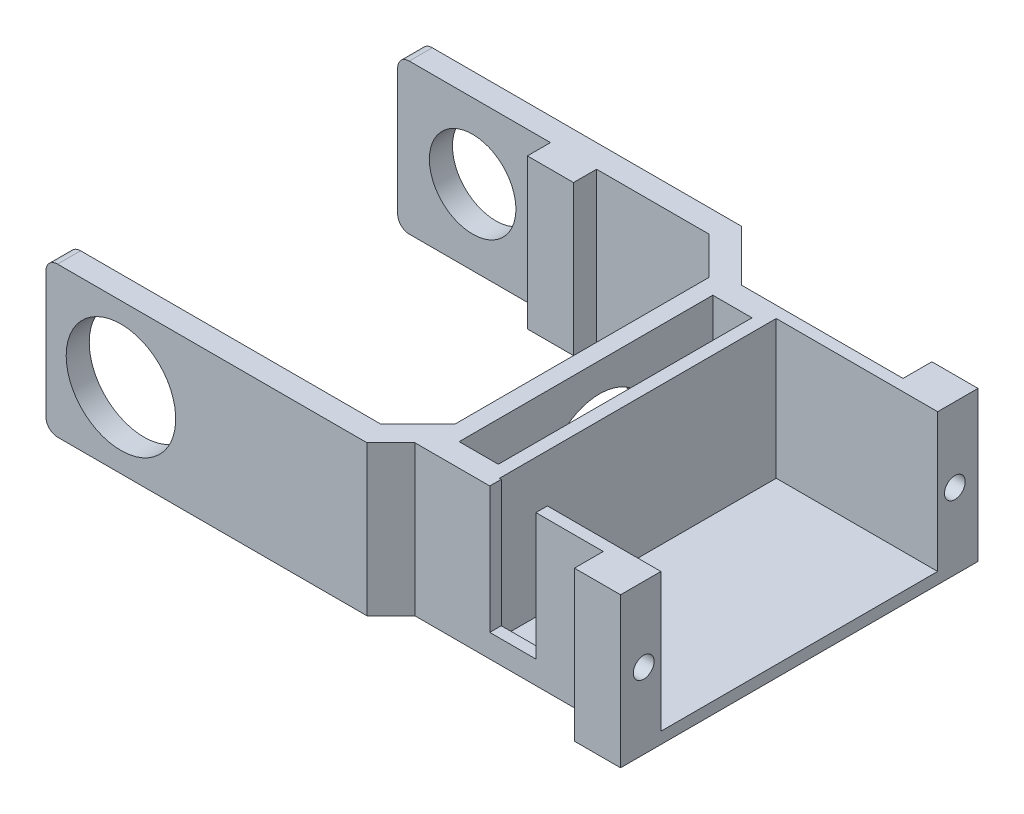
SolidWorks part; units mm, degrees
material "uhlíková ocel 7850"
ref_plane "Přední rovina" through (0, 0, 0) normal (0, 0, 1) x (1, 0, 0)
ref_plane "Horní rovina" through (0, 0, 0) normal (0, 1, 0) x (1, 0, 0)
ref_plane "Pravá rovina" through (0, 0, 0) normal (1, 0, 0) x (0, 0, -1)
sketch "Skica1" plane through (0, 0, 0) normal (0, 1, 0) x (1, 0, 0)
  line L0 (0, -11) -> (0, 11)
  line L1 (0, 11) -> (-3.25, 14.25)
  line L2 (-3.25, 14.25) -> (-30.25, 14.25)
  line L3 (-30.25, 14.25) -> (-30.25, 16.25)
  line L4 (-30.25, 16.25) -> (-2.4216, 16.25)
  line L5 (-2.4216, 16.25) -> (2, 11.8284)
  line L6 (2, 11.8284) -> (2, -11.8284)
  line L7 (2, 0) -> (0, 0) construction
  line L8 (-2.4216, -16.25) -> (2, -11.8284)
  line L9 (-30.25, -16.25) -> (-2.4216, -16.25)
  line L10 (-30.25, -14.25) -> (-30.25, -16.25)
  line L11 (-3.25, -14.25) -> (-30.25, -14.25)
  line L12 (0, -11) -> (-3.25, -14.25)
  dimension "D1" = 11
  dimension "D2" = 135
  dimension "D3" = 27
  dimension "D4" = 2
  dimension "D5" = 2
  dimension "D6" = 2
  dimension "D7" = 14.25
extrude "Přidat vysunutím1" add sketch "Skica1" along normal blind 13
fillet "Zaoblit1" radius 1 4 edges at (-30.25, 0, -15.25) (-30.25, 0, 15.25) (-30.25, 13, 15.25) (-30.25, 13, -15.25)
sketch "Skica6" plane through (0, 0, -16.25) normal (0, 0, -1) x (-1, 0, 0)
  line L0 (23.75, 6.5) -> (30.25, 6.5) construction
  line L1 (30.25, 12) -> (30.25, 1) construction
  circle A0 centre (23.75, 6.5) radius 3.75
  dimension "D1" = 7.5
  dimension "D2" = 6.5
extrude "Odebrat vysunutím4" cut sketch "Skica6" against normal blind 5
sketch "Skica7" plane through (0, 0, 14.25) normal (0, 0, -1) x (-1, 0, 0)
  circle A0 centre (23.75, 6.5) radius 4.75
  dimension "D1" = 9.5
extrude "Odebrat vysunutím5" cut sketch "Skica7" against normal blind 5
sketch "Skica8" plane through (0, 0, 0) normal (0, -1, 0) x (1, 0, 0)
  line L0 (-2.4216, 16.25) -> (2, 11.8284) construction
  line L1 (-0.3431, 14.1716) -> (20, 14.1716)
  line L2 (2, -11.8284) -> (2, 11.8284)
  line L3 (2, -11.8284) -> (20, -11.8284)
  line L4 (20, 14.1716) -> (20, -11.8284)
  line L5 (2, 11.8284) -> (-0.3431, 14.1716)
  line L6 (0, -11) -> (0, 11) construction
  line L7 (2, -11.8284) -> (-2.4216, -16.25) construction
  dimension "D1" = 20
  dimension "D2" = 26
extrude "Přidat vysunutím2" add sketch "Skica8" against normal up to surface (13 mm away) up to face at (-10.3619, 13, 0)
sketch "Skica9" plane through (0, 13, 0) normal (0, 1, 0) x (1, 0, 0)
  line L0 (0, -1.1716) -> (22.3835, -1.1716) construction
  line L1 (0, 11) -> (0, -11) construction
  line L2 (20, 11.8284) -> (2, 11.8284) construction
  line L3 (1.5, -12.1716) -> (4.9, -12.1716)
  line L4 (1.5, -12.1716) -> (1.5, 9.8284)
  line L5 (1.5, 9.8284) -> (4.9, 9.8284)
  line L6 (4.9, -12.1716) -> (4.9, 9.8284)
  line L7 (1.5, -12.1716) -> (4.9, 9.8284) construction
  line L8 (1.5, 9.8284) -> (4.9, -12.1716) construction
  line L9 (-0.3431, -14.1716) -> (20, -14.1716) construction
  point P4 (3.2, -1.1716)
  dimension "D1" = 1.5
  dimension "D2" = 2
  dimension "D3" = 3.4
  dimension "D4" = 2
extrude "Odebrat vysunutím6" cut sketch "Skica9" against normal through all
sketch "Skica10" plane through (0, 13, 0) normal (0, 1, 0) x (1, 0, 0)
  line L0 (20, -14.1716) -> (20, 11.8284) construction
  line L1 (20, 10.8284) -> (6, 10.8284)
  line L2 (20, 10.8284) -> (20, -13.1716)
  line L3 (20, -13.1716) -> (6, -13.1716)
  line L4 (6, 10.8284) -> (6, -13.1716)
  line L6 (-0.3431, -14.1716) -> (20, -14.1716) construction
  dimension "D1" = 24
  dimension "D2" = 1
  dimension "D3" = 14
extrude "Odebrat vysunutím7" cut sketch "Skica10" against normal blind 12
sketch "Skica11" plane through (20, 0, 0) normal (1, 0, 0) x (0, 0, -1)
  line L0 (-16.25, 0) -> (-14.1716, 0) construction
  line L1 (-14.1716, 13) -> (-16.6716, 13)
  line L2 (-14.1716, 13) -> (-14.1716, 0)
  line L3 (-14.1716, 0) -> (-16.6716, 0)
  line L4 (-16.6716, 13) -> (-16.6716, 0)
  line L5 (11.8284, 0) -> (16.25, 0) construction
  line L6 (11.8284, 13) -> (14.3284, 13)
  line L7 (11.8284, 13) -> (11.8284, 0)
  line L8 (11.8284, 0) -> (14.3284, 0)
  line L9 (14.3284, 13) -> (14.3284, 0)
  dimension "D1" = 2.5
extrude "Přidat vysunutím3" add sketch "Skica11" against normal blind 4
sketch "Skica12" plane through (20, 0, 0) normal (1, 0, 0) x (0, 0, -1)
  circle A0 centre (-14.6654, 6.5551) radius 0.9
  circle A1 centre (12.3221, 6.5551) radius 0.9
  dimension "D1" = 1.8
extrude "Odebrat vysunutím8" cut sketch "Skica12" against normal blind 4
sketch "Skica13" plane through (0, 0, 14.1716) normal (0, 0, 1) x (1, 0, 0)
  line L0 (-0.3431, 13) -> (16, 13) construction
  line L1 (6.1569, 13) -> (10.1569, 13)
  line L2 (6.1569, 13) -> (6.1569, 2)
  line L3 (6.1569, 2) -> (10.1569, 2)
  line L4 (10.1569, 13) -> (10.1569, 2)
  line L5 (-0.3431, 13) -> (-0.3431, 0) construction
  dimension "D1" = 4
  dimension "D2" = 11
  dimension "D3" = 6.5
extrude "Odebrat vysunutím9" cut sketch "Skica13" against normal blind 4
sketch "Skica14" plane through (0, 0, 0) normal (-1, 0, 0) x (0, 0, 1)
  line L0 (0, 6) -> (0, 0) construction
  line L1 (-11, 0) -> (11, 0) construction
  circle A0 centre (0, 6) radius 4.5
  dimension "D1" = 9
  dimension "D2" = 6
extrude "Odebrat vysunutím10" cut sketch "Skica14" against normal blind 4
sketch "Skica15" plane through (0, 13, 0) normal (0, 1, 0) x (1, 0, 0)
  line L2 (-13, 14.25) -> (-17, 14.25)
  line L3 (-13, 14.25) -> (-13, 12.25)
  line L4 (-13, 12.25) -> (-17, 12.25)
  line L5 (-17, 14.25) -> (-17, 12.25)
  line L6 (-15, 11.25) -> (-15, 12.8936) construction
  line L7 (-29.25, 14.25) -> (-3.25, 14.25) construction
  line L8 (0, 11) -> (0, -11) construction
  dimension "D1" = 2
  dimension "D2" = 4
  dimension "D3" = 2
  dimension "D4" = 15
extrude "Přidat vysunutím4" add sketch "Skica15" against normal up to surface (13 mm away) up to face at (3.2, 0, 1.1716)
